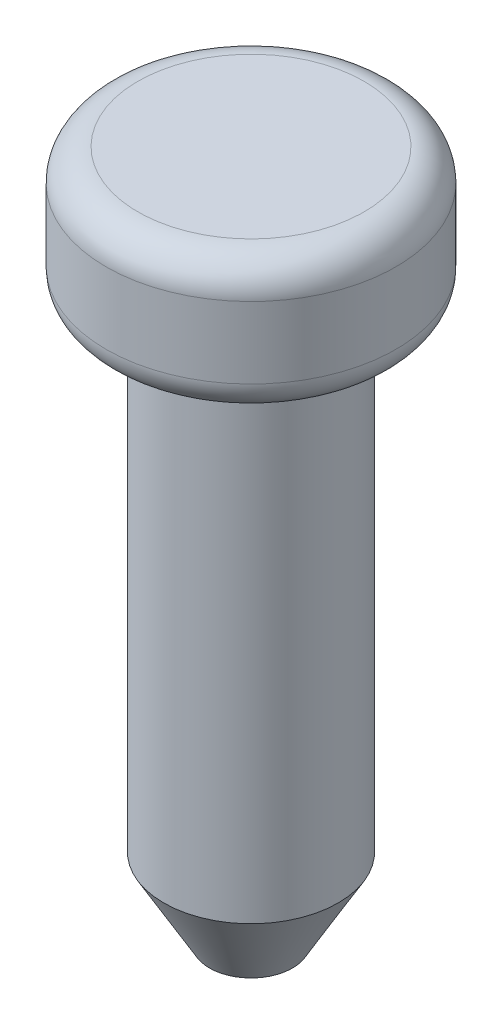
SolidWorks part; units mm, degrees
ref_plane "Front Plane" through (0, 0, 0) normal (0, 0, 1) x (1, 0, 0)
ref_plane "Top Plane" through (0, 0, 0) normal (0, 1, 0) x (1, 0, 0)
ref_plane "Right Plane" through (0, 0, 0) normal (1, 0, 0) x (0, 0, -1)
sketch "Sketch1" plane through (0, 0, 0) normal (0, 0, 1) x (1, 0, 0)
  line L0 (0, 0) -> (0, 8.7)
  line L1 (0, 8.7) -> (-1.825, 8.7)
  line L2 (-1.825, 8.7) -> (-1.825, 7)
  line L3 (-1.825, 7) -> (-1.1, 7)
  line L4 (-1.1, 7) -> (-1.1, 0)
  line L5 (-1.1, 0) -> (0, 0)
  dimension "D1" = 7
  dimension "D2" = 1.1
  dimension "D3" = 1.7
  dimension "D4" = 1.825
revolve "Revolve2" add sketch "Sketch1" angle 360 about L0
fillet "Fillet1" radius 0.4 2 edges at (0, 7, -1.825) (0, 8.7, -1.825)
chamfer "Chamfer1" distance 1 angle 30 1 edges at (0, 0, -1.1)
